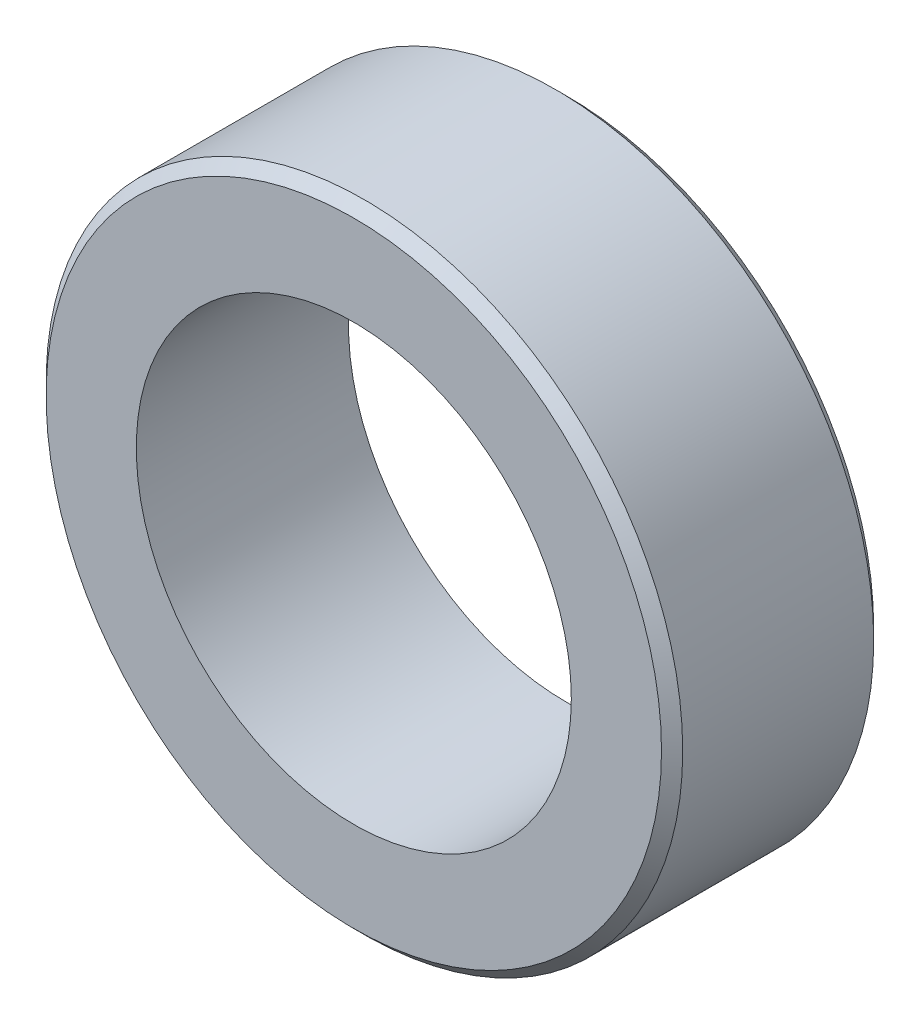
SolidWorks part; units mm, degrees
material "1060 合金"
ref_plane "前视基准面" through (0, 0, 0) normal (0, 0, 1) x (1, 0, 0)
ref_plane "上视基准面" through (0, 0, 0) normal (0, 1, 0) x (1, 0, 0)
ref_plane "右视基准面" through (0, 0, 0) normal (1, 0, 0) x (0, 0, -1)
other "Configuration Table"
sketch "草图1" plane through (0, 0, 0) normal (0, 0, 1) x (1, 0, 0)
  circle A0 centre (0, 0) radius 2.05
  circle A1 centre (0, 0) radius 3
  dimension "D1" = 4.1
  dimension "D2" = 6
extrude "凸台-拉伸1" add sketch "草图1" along normal blind 2
chamfer "倒角1" distance 0.1 angle 45 2 edges at (3, 0, 2) (3, 0, 0)
